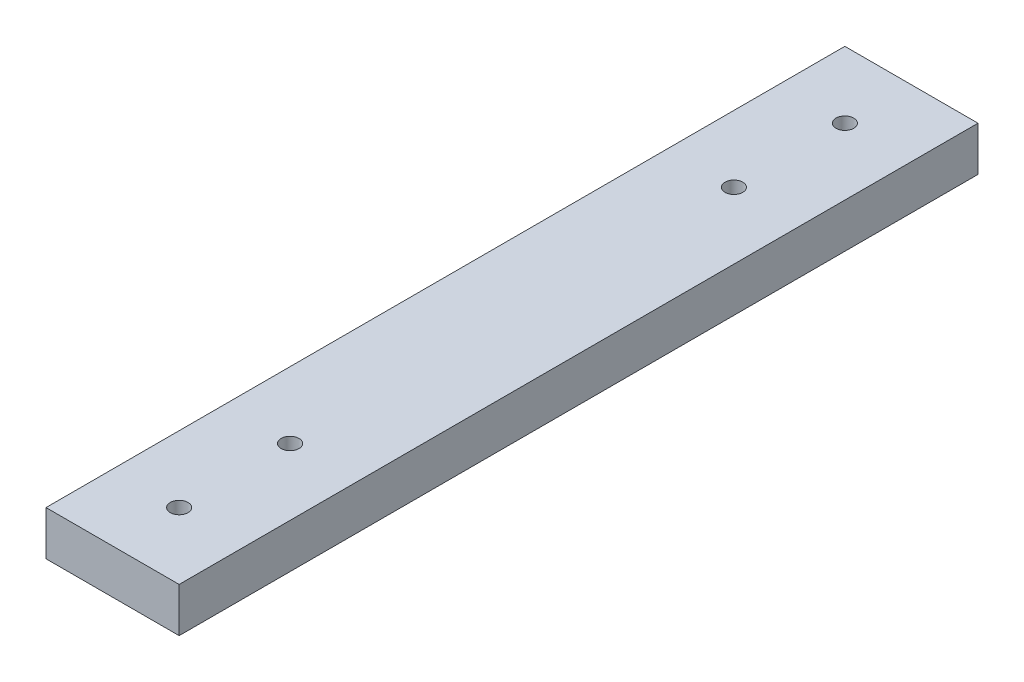
SolidWorks part; units mm, degrees
ref_plane "Front Plane" through (0, 0, 0) normal (0, 0, 1) x (1, 0, 0)
ref_plane "Top Plane" through (0, 0, 0) normal (0, 1, 0) x (1, 0, 0)
ref_plane "Right Plane" through (0, 0, 0) normal (1, 0, 0) x (0, 0, -1)
sketch "Sketch1" plane through (0, 0, 0) normal (0, 1, 0) x (1, 0, 0)
  line L56 (0, 0) -> (30, 0)
  line L57 (0, 0) -> (0, 180)
  line L58 (0, 180) -> (30, 180)
  line L59 (30, 0) -> (30, 180)
  circle A13 centre (15, 15) radius 2
  circle A14 centre (15, 140) radius 2
  circle A15 centre (15, 40) radius 2
  circle A16 centre (15, 165) radius 2
extrude "Boss-Extrude1" add sketch "Sketch1" along normal blind 10
